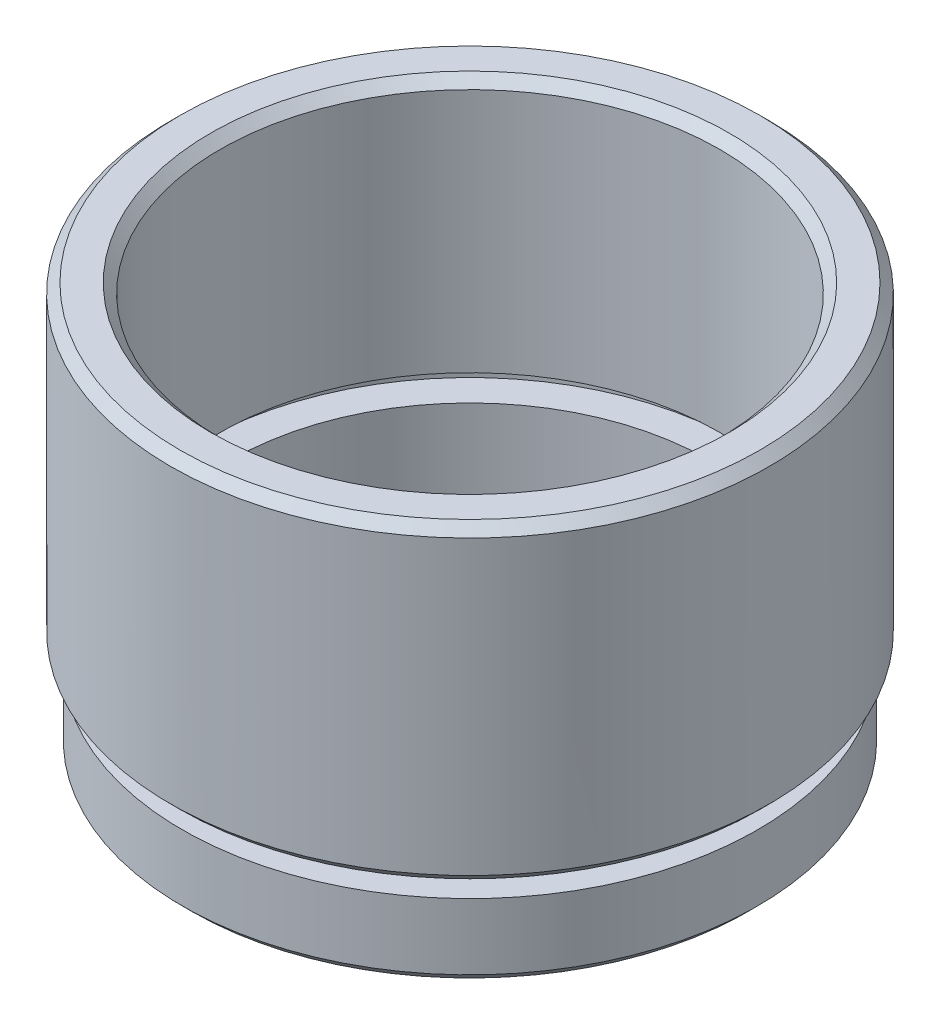
SolidWorks part; units mm, degrees
ref_plane "前视基准面" through (0, 0, 0) normal (0, 0, 1) x (1, 0, 0)
ref_plane "上视基准面" through (0, 0, 0) normal (0, 1, 0) x (1, 0, 0)
ref_plane "右视基准面" through (0, 0, 0) normal (1, 0, 0) x (0, 0, -1)
sketch "草图1" plane through (0, 0, 0) normal (0, 0, 1) x (1, 0, 0)
  line L0 (0, 0) -> (0, 21.8535) construction
  line L1 (12, 0) -> (15.25, 0)
  line L2 (15.25, 0) -> (15.25, 4)
  line L3 (15.25, 4) -> (13.75, 4)
  line L4 (13.75, 4) -> (13.75, 5)
  line L5 (13.75, 5) -> (15.875, 5)
  line L6 (15.875, 5) -> (15.875, 21.5)
  line L7 (15.875, 21.5) -> (13.25, 21.5)
  line L8 (13.25, 21.5) -> (13.25, 8)
  line L9 (13.25, 8) -> (14.35, 8)
  line L10 (14.35, 8) -> (14.35, 7)
  line L11 (14.35, 7) -> (12.7, 7)
  line L12 (12.7, 7) -> (12.7, 2)
  line L13 (12.7, 2) -> (12, 2)
  line L14 (12, 0) -> (12, 2)
  dimension "D1" = 21.5
  dimension "D2" = 15.875
  dimension "D3" = 13.25
  dimension "D4" = 12.7
  dimension "D5" = 1
  dimension "D6" = 5
  dimension "D7" = 12
  dimension "D8" = 15.25
  dimension "D9" = 1
  dimension "D10" = 5
  dimension "D11" = 2
  dimension "D12" = 14.35
  dimension "D13" = 13.75
revolve "旋转1" add sketch "草图1" angle 360 about L0
cosmetic thread "装饰螺纹线11" parameters "D2"=28.5
cosmetic thread "装饰螺纹线12" parameters "D2"=28.5
chamfer "倒角1" distance 0.5 angle 45 4 edges at (0, 21.5, -13.25) (0, 21.5, -15.875) (0, 5, -15.875) (0, 0, -15.25)
